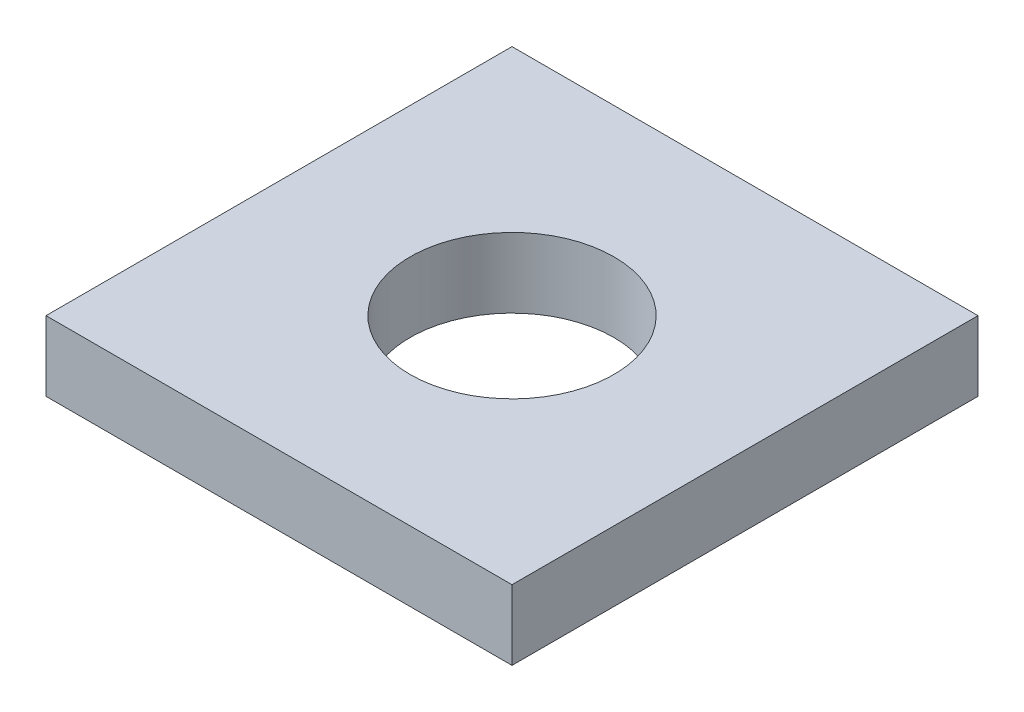
SolidWorks part; units mm, degrees
ref_plane "Front Plane" through (0, 0, 0) normal (0, 0, 1) x (1, 0, 0)
ref_plane "Top Plane" through (0, 0, 0) normal (0, 1, 0) x (1, 0, 0)
ref_plane "Right Plane" through (0, 0, 0) normal (1, 0, 0) x (0, 0, -1)
sketch "Sketch1" plane through (0, 0, 0) normal (0, 1, 0) x (1, 0, 0)
  line L1 (-20, -20) -> (20, -20)
  line L2 (-20, -20) -> (-20, 20)
  line L3 (-20, 20) -> (20, 20)
  line L4 (20, -20) -> (20, 20)
  line L5 (-20, -20) -> (20, 20) construction
  line L6 (-20, 20) -> (20, -20) construction
  circle A0 centre (0, 0) radius 8.75
  point P0 (0, 0)
  dimension "D3" = 17.5
  dimension "D1" = 40
  dimension "D2" = 40
extrude "Boss-Extrude1" add sketch "Sketch1" along normal blind 6
